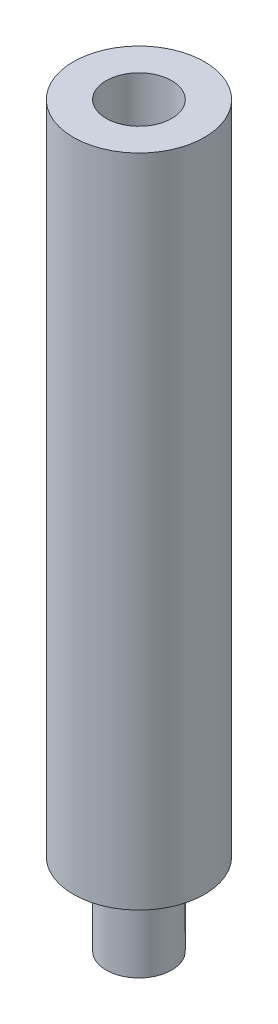
SolidWorks part; units mm, degrees
ref_plane "Plan de face" through (0, 0, 0) normal (0, 0, 1) x (1, 0, 0)
ref_plane "Plan de dessus" through (0, 0, 0) normal (0, 1, 0) x (1, 0, 0)
ref_plane "Plan de droite" through (0, 0, 0) normal (1, 0, 0) x (0, 0, -1)
sketch "Esquisse1" plane through (0, 0, 0) normal (0, 1, 0) x (1, 0, 0)
  circle A1 centre (0, 0) radius 4
  dimension "D2" = 8
extrude "Boss.-Extru.1" add sketch "Esquisse1" against normal blind 40
sketch "Esquisse3" plane through (0, 0, 0) normal (0, 1, 0) x (1, 0, 0)
  circle A0 centre (0, 0) radius 2
  dimension "D1" = 4
extrude "Enlèv. mat.-Extru.1" cut sketch "Esquisse3" against normal blind 10
sketch "Esquisse4" plane through (0, -40, 0) normal (0, -1, 0) x (1, 0, 0)
  circle A0 centre (0, 0) radius 2
  dimension "D1" = 4
extrude "Boss.-Extru.2" add sketch "Esquisse4" along normal blind 5
